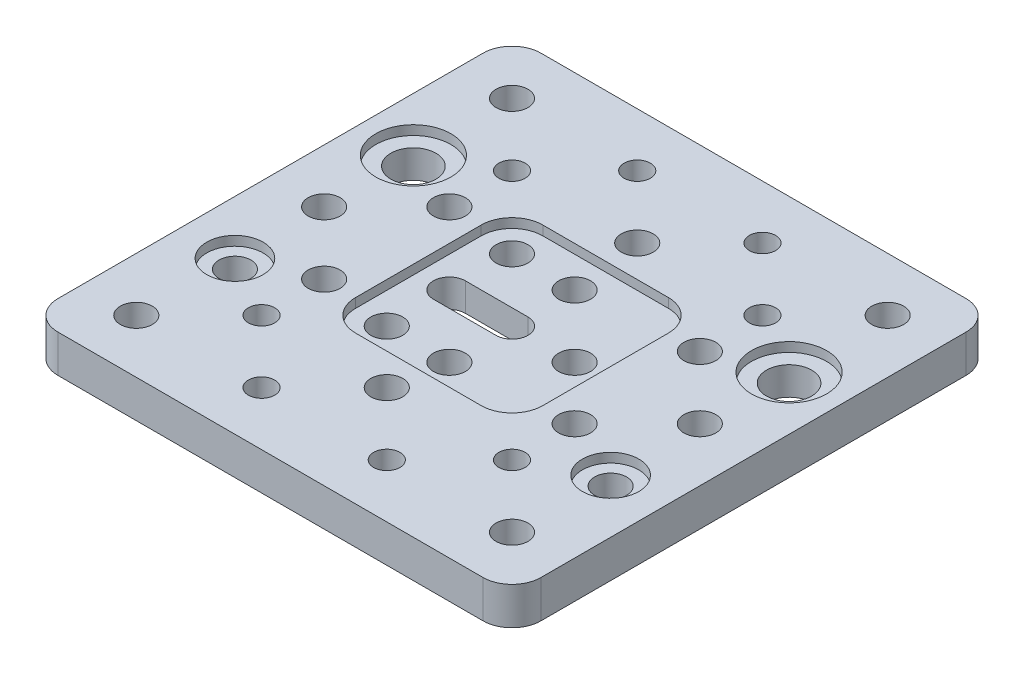
SolidWorks part; units mm, degrees
material "6061-T6 (SS)"
ref_plane "Front Plane" through (0, 0, 0) normal (0, 0, 1) x (1, 0, 0)
ref_plane "Top Plane" through (0, 0, 0) normal (0, 1, 0) x (1, 0, 0)
ref_plane "Right Plane" through (0, 0, 0) normal (1, 0, 0) x (0, 0, -1)
sketch "Sketch1" plane through (0, 0, 0) normal (0, 1, 0) x (1, 0, 0)
  line L0 (-23.7657, 0) -> (0, 0) construction
  line L1 (33.94, -38.575) -> (-33.94, -38.575)
  line L2 (38.575, -33.94) -> (38.575, 33.94)
  line L3 (33.94, 38.575) -> (-33.94, 38.575)
  line L4 (-38.575, -33.94) -> (-38.575, 33.94)
  line L5 (38.575, -38.575) -> (-38.575, 38.575) construction
  line L6 (38.575, 38.575) -> (-38.575, -38.575) construction
  line L7 (0, 0) -> (0, 28.9978) construction
  line L8 (0, 0) -> (-10, 0) construction
  line L9 (0, -2.55) -> (-10, -2.55)
  line L10 (0, 2.55) -> (-10, 2.55)
  arc A0 (-33.94, 38.575) -> (-38.575, 33.94) centre (-33.94, 33.94) ccw
  arc A1 (38.575, 33.94) -> (33.94, 38.575) centre (33.94, 33.94) ccw
  arc A2 (-33.94, -38.575) -> (-38.575, -33.94) centre (-33.94, -33.94) cw
  arc A3 (33.94, -38.575) -> (38.575, -33.94) centre (33.94, -33.94) ccw
  circle A4 centre (-30, 14.25) radius 3.6
  circle A5 centre (-20, 10) radius 2.55
  circle A7 centre (0, 20) radius 2.55
  circle A8 centre (0, 10) radius 2.55
  circle A9 centre (-10, 10) radius 2.55
  circle A11 centre (-30, 30) radius 2.55
  circle A12 centre (-30, 0) radius 2.55
  circle A13 centre (30, 30) radius 2.55
  circle A16 centre (30, 14.25) radius 3.6
  circle A17 centre (30, 0) radius 2.55
  circle A18 centre (20, 10) radius 2.55
  circle A19 centre (20, -10) radius 2.55
  circle A21 centre (-30, -30) radius 2.55
  circle A22 centre (30, -30) radius 2.55
  circle A25 centre (-20, -10) radius 2.55
  circle A27 centre (0, -20) radius 2.55
  circle A28 centre (0, -10) radius 2.55
  circle A29 centre (-10, -10) radius 2.55
  circle A30 centre (10, 0) radius 2.55
  arc A31 (0, -2.55) -> (0, 2.55) centre (0, 0) ccw
  arc A32 (-10, 2.55) -> (-10, -2.55) centre (-10, 0) ccw
  circle A33 centre (30, -14.25) radius 2.55
  circle A34 centre (-30, -14.25) radius 2.55
  point P0 (0, 0)
  point P25 (0, 0)
  point P26 (0, 0)
  point P75 (-5, 0)
  dimension "D2" = 4.635
  dimension "D3" = 5.1
  dimension "D4" = 7.2
  dimension "D12" = 10
  dimension "D1" = 77.15
  dimension "D5" = 40
  dimension "D6" = 60
  dimension "D7" = 40
  dimension "D9" = 20
  dimension "D10" = 28.5
  dimension "D11" = 60
  dimension "D13" = 10
  dimension "D14" = 10
  dimension "D15" = 5.1
extrude "Boss-Extrude1" add sketch "Sketch1" along normal blind 6
hole_wizard "M5x0.8 Tapped Hole1" positions "Sketch4" profile "Sketch3" tap size "M5x0.8" standard "ANSI Metric" end condition through all
sketch "Sketch4" plane through (0, 6, 0) normal (0, 1, 0) x (1, 0, 0)
  line L0 (-17.7377, 0) -> (0, 0) construction
  line L1 (0, 0) -> (0, 30.1375) construction
  point P0 (-20, 20)
  point P2 (-10, 30)
  point P11 (10, 30)
  point P12 (20, 20)
  point P13 (20, -20)
  point P14 (10, -30)
  point P15 (-10, -30)
  point P16 (-20, -20)
  point P17 (0, 0)
  point P18 (0, 0)
  point P19 (0, 0)
  point P20 (0, 0)
  dimension "D1" = 20
  dimension "D2" = 40
  dimension "D3" = 40
  dimension "D4" = 60
sketch "Sketch3" plane through (-20, 6, -20) normal (1, 0, 0) x (0, 0, 1)
  line L0 (0, 0) -> (0, 6)
  line L1 (0, 6) -> (2.1, 6)
  line L2 (2.1, 6) -> (2.1, 0)
  line L5 (2.1, 0) -> (0, 0)
  line L11 (0, -6.35) -> (0, 107.95) construction
  dimension "Thru Tap Drill Dia." = 4.2
  dimension "Thru Tap Drill Depth" = 6
cosmetic thread "Hole Thread1" parameters "D2"=5
cosmetic thread "Hole Thread2" parameters "D2"=5
cosmetic thread "Hole Thread3" parameters "D2"=5
cosmetic thread "Hole Thread4" parameters "D2"=5
cosmetic thread "Hole Thread5" parameters "D2"=5
cosmetic thread "Hole Thread6" parameters "D2"=5
cosmetic thread "Hole Thread7" parameters "D2"=5
cosmetic thread "Hole Thread8" parameters "D2"=5
sketch "Sketch2" plane through (0, 6, 0) normal (0, 1, 0) x (1, 0, 0)
  line L1 (10.03, -14.95) -> (-10.03, -14.95)
  line L2 (14.95, -10.03) -> (14.95, 10.03)
  line L3 (10.03, 14.95) -> (-10.03, 14.95)
  line L4 (-14.95, -10.03) -> (-14.95, 10.03)
  line L5 (14.95, -14.95) -> (-14.95, 14.95) construction
  line L6 (14.95, 14.95) -> (-14.95, -14.95) construction
  circle A0 centre (-30, 14.25) radius 6
  circle A1 centre (30, 14.25) radius 6
  circle A2 centre (30, -14.25) radius 4.5
  circle A3 centre (-30, -14.25) radius 4.5
  arc A4 (-10.03, 14.95) -> (-14.95, 10.03) centre (-10.03, 10.03) ccw
  arc A5 (10.03, -14.95) -> (14.95, -10.03) centre (10.03, -10.03) ccw
  arc A6 (14.95, 10.03) -> (10.03, 14.95) centre (10.03, 10.03) ccw
  arc A7 (-10.03, -14.95) -> (-14.95, -10.03) centre (-10.03, -10.03) cw
  point P12 (0, 0)
  dimension "D1" = 12
  dimension "D2" = 9
  dimension "D4" = 4.92
  dimension "D3" = 29.9
extrude "Cut-Extrude1" cut sketch "Sketch2" against normal blind 1.5
